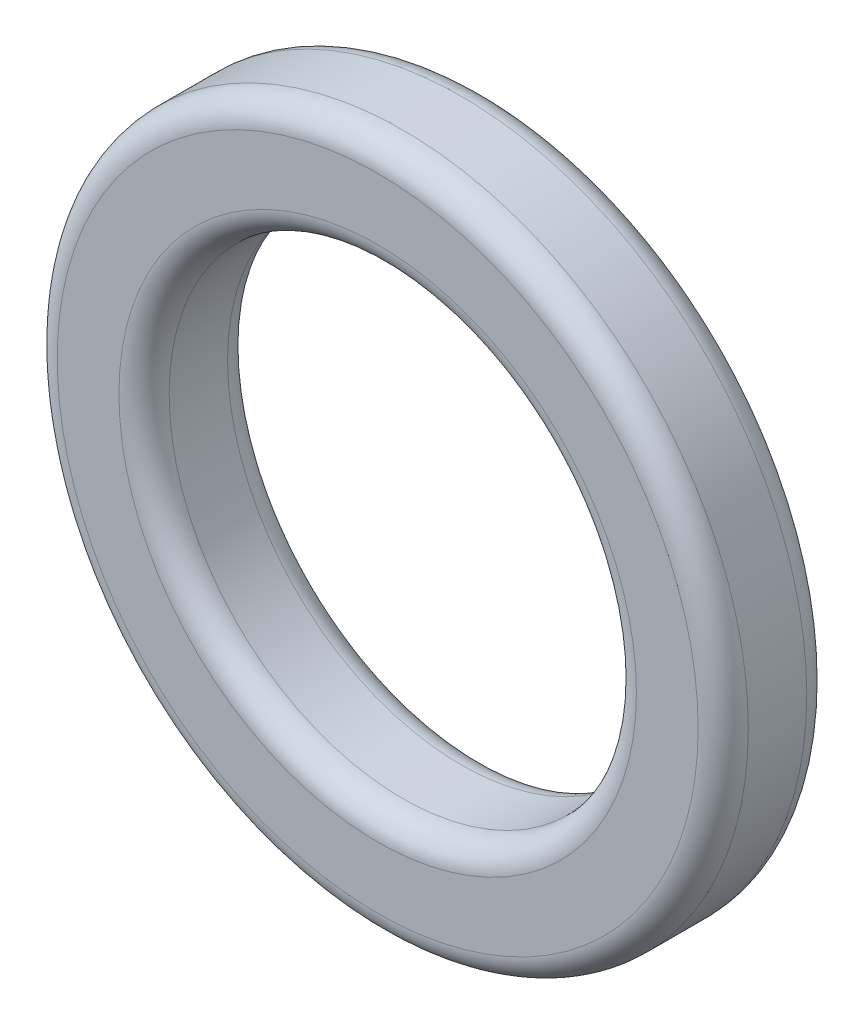
SolidWorks part; units mm, degrees
ref_plane "Front Plane" through (0, 0, 0) normal (0, 0, 1) x (1, 0, 0)
ref_plane "Top Plane" through (0, 0, 0) normal (0, 1, 0) x (1, 0, 0)
ref_plane "Right Plane" through (0, 0, 0) normal (1, 0, 0) x (0, 0, -1)
sketch "Sketch2" plane through (0, 0, 0) normal (0, 0, 1) x (1, 0, 0)
  circle A0 centre (0, 0) radius 13.775
  circle A1 centre (0, 0) radius 9.315
  dimension "D1" = 27.55
  dimension "D2" = 18.63
extrude "Boss-Extrude1" add sketch "Sketch2" along normal blind 4.33
fillet "Fillet2" radius 1 4 edges at (9.315, 0, 0) (13.775, 0, 0) (9.315, 0, 4.33) (13.775, 0, 4.33)
